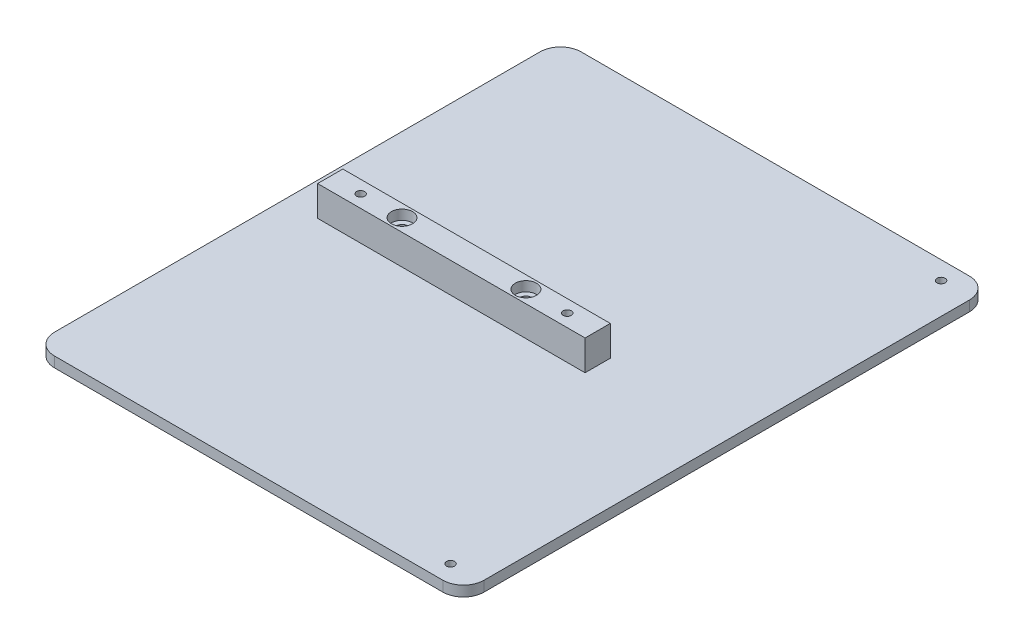
SolidWorks part; units mm, degrees
ref_plane "Front Plane" through (0, 0, 0) normal (0, 0, 1) x (1, 0, 0)
ref_plane "Top Plane" through (0, 0, 0) normal (0, 1, 0) x (1, 0, 0)
ref_plane "Right Plane" through (0, 0, 0) normal (1, 0, 0) x (0, 0, -1)
sketch "Sketch1" plane through (0, 0, 0) normal (0, 1, 0) x (1, 0, 0)
  line L1 (66.04, -80.9625) -> (-66.04, -80.9625)
  line L2 (66.04, -80.9625) -> (66.04, 80.9625)
  line L3 (66.04, 80.9625) -> (-66.04, 80.9625)
  line L4 (-66.04, -80.9625) -> (-66.04, 80.9625)
  line L5 (66.04, -80.9625) -> (-66.04, 80.9625) construction
  line L6 (66.04, 80.9625) -> (-66.04, -80.9625) construction
  point P0 (0, 0)
  dimension "D1" = 161.925
  dimension "D2" = 132.08
extrude "Boss-Extrude1" add sketch "Sketch1" along normal blind 3.175
fillet "Fillet1" radius 6.35 4 edges at (-66.04, 1.5875, -80.9625) (66.04, 1.5875, -80.9625) (66.04, 1.5875, 80.9625) (-66.04, 1.5875, 80.9625)
hole_wizard "Tap Drill for M3x0.5 Tap1" positions "Sketch2" profile "Sketch3" hole size "M3x0.5" standard "ANSI Metric" end condition through all
sketch "Sketch2" plane through (0, 3.175, 0) normal (0, 1, 0) x (1, 0, 0)
  point P0 (56.515, -75.4062)
  point P3 (56.515, 75.4062)
sketch "Sketch3" plane through (56.515, 3.175, 75.4062) normal (1, 0, 0) x (0, 0, 1)
  line L0 (0, 0) -> (0, 3.175)
  line L1 (0, 3.175) -> (1.25, 3.175)
  line L2 (1.25, 3.175) -> (1.25, 0)
  line L5 (1.25, 0) -> (0, 0)
  line L11 (0, -6.35) -> (0, 107.95) construction
  dimension "Thru Hole Dia." = 2.5
  dimension "Thru Hole Depth" = 3.175
sketch "Sketch5" plane through (0, 3.175, 0) normal (0, 1, 0) x (1, 0, 0)
  line L0 (26.3398, -2.7686) -> (-55.88, -2.7686) construction
  line L1 (26.3398, 2.7686) -> (-55.88, 2.7686) construction
  line L2 (26.3398, -2.7686) -> (-55.88, -2.7686) construction
  line L3 (26.3398, 2.7686) -> (-55.88, 2.7686) construction
  line L4 (-14.7701, 2.7686) -> (-14.7701, -2.7686) construction
  line L5 (-55.88, 4.1275) -> (26.3398, 4.1275) construction
  line L6 (26.3431, -3.8735) -> (-55.8833, -3.8735)
  line L7 (26.3431, -3.8735) -> (26.3431, 3.8735)
  line L8 (26.3431, 3.8735) -> (-55.8833, 3.8735)
  line L9 (-55.8833, -3.8735) -> (-55.8833, 3.8735)
  line L10 (26.3431, -3.8735) -> (-55.8833, 3.8735) construction
  line L11 (26.3431, 3.8735) -> (-55.8833, -3.8735) construction
  point P6 (-14.7701, 0)
  dimension "D1" = 0.254
extrude "Boss-Extrude2" add sketch "Sketch5" along normal blind 9.271
hole_wizard "Tap Drill for M3x0.5 Tap2" positions "Sketch6" profile "Sketch7" hole size "M3x0.5" standard "ANSI Metric" end condition through all
sketch "Sketch6" plane through (0, 12.446, 0) normal (0, 1, 0) x (1, 0, 0)
  point P0 (-46.5201, 0)
  point P3 (16.9799, 0)
sketch "Sketch7" plane through (-46.5201, 12.446, 0) normal (1, 0, 0) x (0, 0, 1)
  line L0 (0, 0) -> (0, 12.446)
  line L1 (0, 12.446) -> (1.25, 12.446)
  line L2 (1.25, 12.446) -> (1.25, 0)
  line L5 (1.25, 0) -> (0, 0)
  line L11 (0, -6.35) -> (0, 107.95) construction
  dimension "Thru Hole Dia." = 2.5
  dimension "Thru Hole Depth" = 12.446
hole_wizard "CBORE for M3 SHCS1" positions "Sketch8" profile "Sketch10" counterbore size "M3" standard "ANSI Metric" end condition through all
sketch "Sketch8" plane through (0, 12.446, 0) normal (0, 1, 0) x (1, 0, 0)
  line L0 (-14.7701, 3.8735) -> (-14.7701, -3.8735) construction
  line L1 (26.3431, 3.8735) -> (-55.8833, 3.8735) construction
  line L2 (-55.8833, -3.8735) -> (26.3431, -3.8735) construction
  line L4 (-33.8201, 0) -> (4.2799, 0) construction
  point P9 (-33.8201, 0)
  point P10 (4.2799, 0)
  point P13 (-14.7701, 0)
  dimension "D1" = 38.1
sketch "Sketch10" plane through (4.2799, 12.446, 0) normal (1, 0, 0) x (0, 0, 1)
  line L0 (0, 0) -> (0, 12.446)
  line L1 (0, 12.446) -> (1.7, 12.446)
  line L3 (1.7, 12.446) -> (1.7, 3)
  line L4 (1.7, 3) -> (3.25, 3)
  line L5 (3.25, 3) -> (3.25, 0)
  line L7 (3.25, 0) -> (0, 0)
  line L11 (0, -6.35) -> (0, 107.95) construction
  dimension "Thru Hole Dia." = 3.4
  dimension "Thru Hole Depth" = 12.446
  dimension "C'Bore Dia." = 6.5
  dimension "C'Bore Depth" = 3
